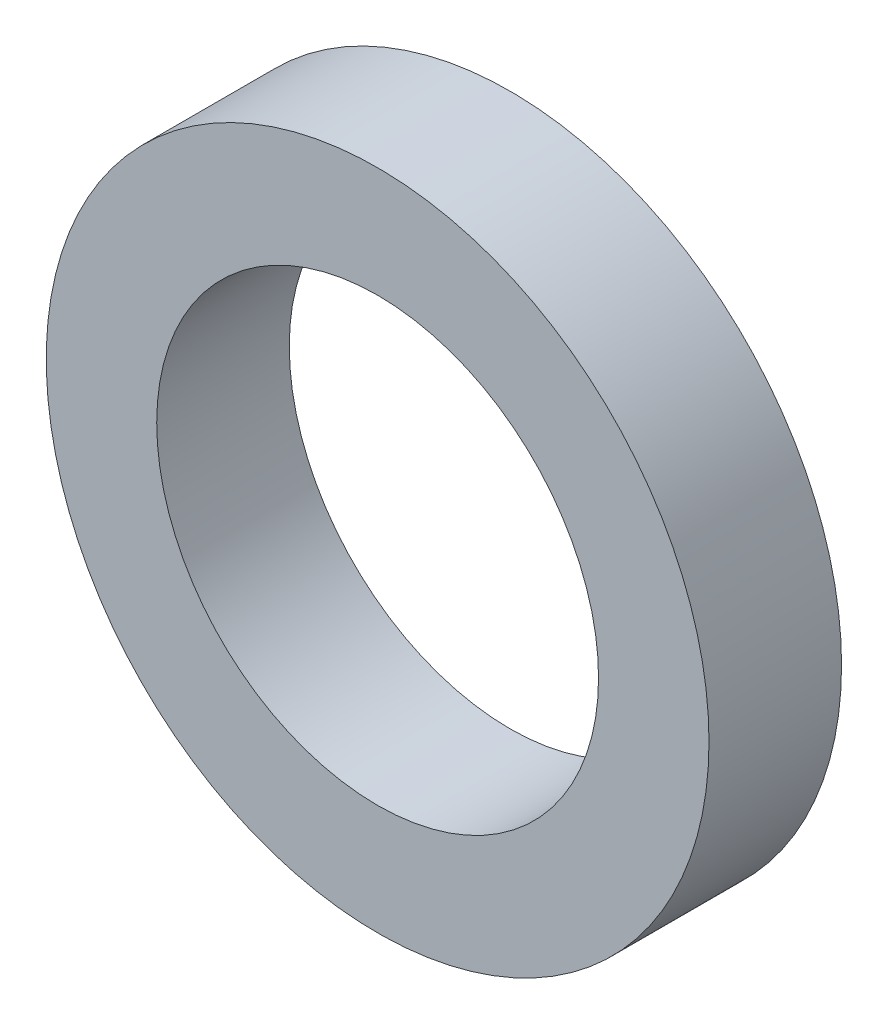
SolidWorks part; units mm, degrees
ref_plane "Front Plane" through (0, 0, 0) normal (0, 0, 1) x (1, 0, 0)
ref_plane "Top Plane" through (0, 0, 0) normal (0, 1, 0) x (1, 0, 0)
ref_plane "Right Plane" through (0, 0, 0) normal (1, 0, 0) x (0, 0, -1)
sketch "Sketch1" plane through (0, 0, 0) normal (0, 0, 1) x (1, 0, 0)
  circle A0 centre (0, 0) radius 5
  circle A1 centre (0, 0) radius 7.5
  dimension "D1" = 10
  dimension "D2" = 15
extrude "Boss-Extrude1" add sketch "Sketch1" along normal blind 3
